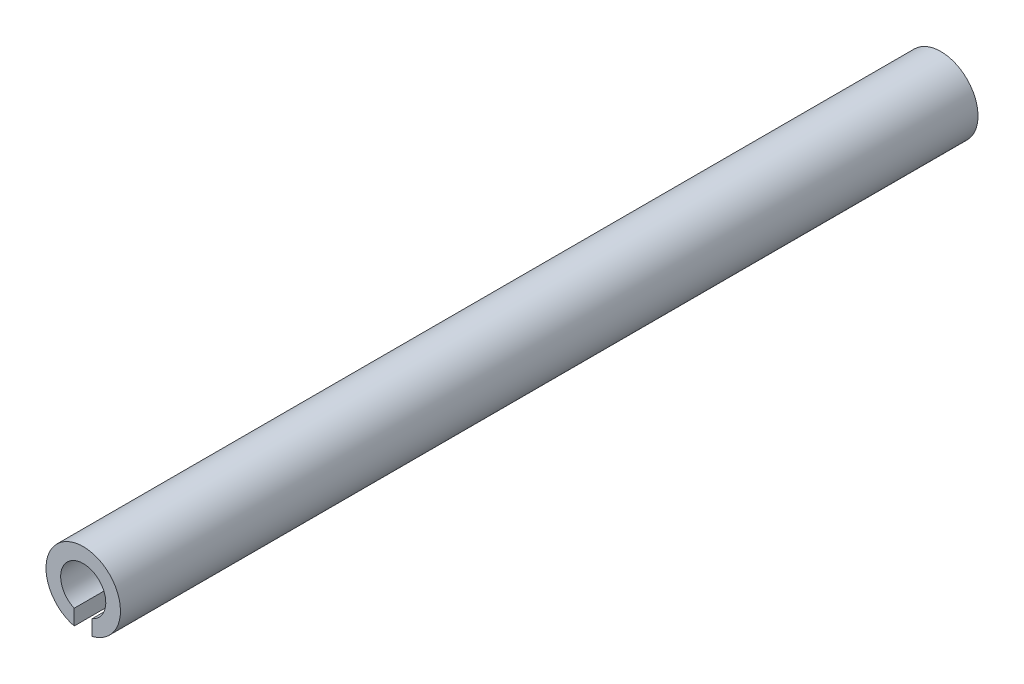
SolidWorks part; units mm, degrees
ref_plane "Front Plane" through (0, 0, 0) normal (0, 0, 1) x (1, 0, 0)
ref_plane "Top Plane" through (0, 0, 0) normal (0, 1, 0) x (1, 0, 0)
ref_plane "Right Plane" through (0, 0, 0) normal (1, 0, 0) x (0, 0, -1)
sketch "Sketch1" plane through (0, 0, 0) normal (0, 0, 1) x (1, 0, 0)
  line L1 (-0.4, 0) -> (0.4, 0)
  line L2 (-0.4, 0) -> (-0.4, -2.2024)
  line L3 (-0.4, -2.2024) -> (0.4, -2.2024)
  line L4 (0.4, 0) -> (0.4, -2.2024)
  circle A0 centre (0, 0) radius 1.65
  circle A1 centre (0, 0) radius 1
  dimension "D1" = 3.3
  dimension "D2" = 2
  dimension "D4" = 0.4
  dimension "D3" = 0.8
  dimension "D5" = 2.2024
  dimension "D6" = 0.4
extrude "dowel_body" add sketch "Sketch1" along normal blind 38 contours A1 L4 A0 L2
